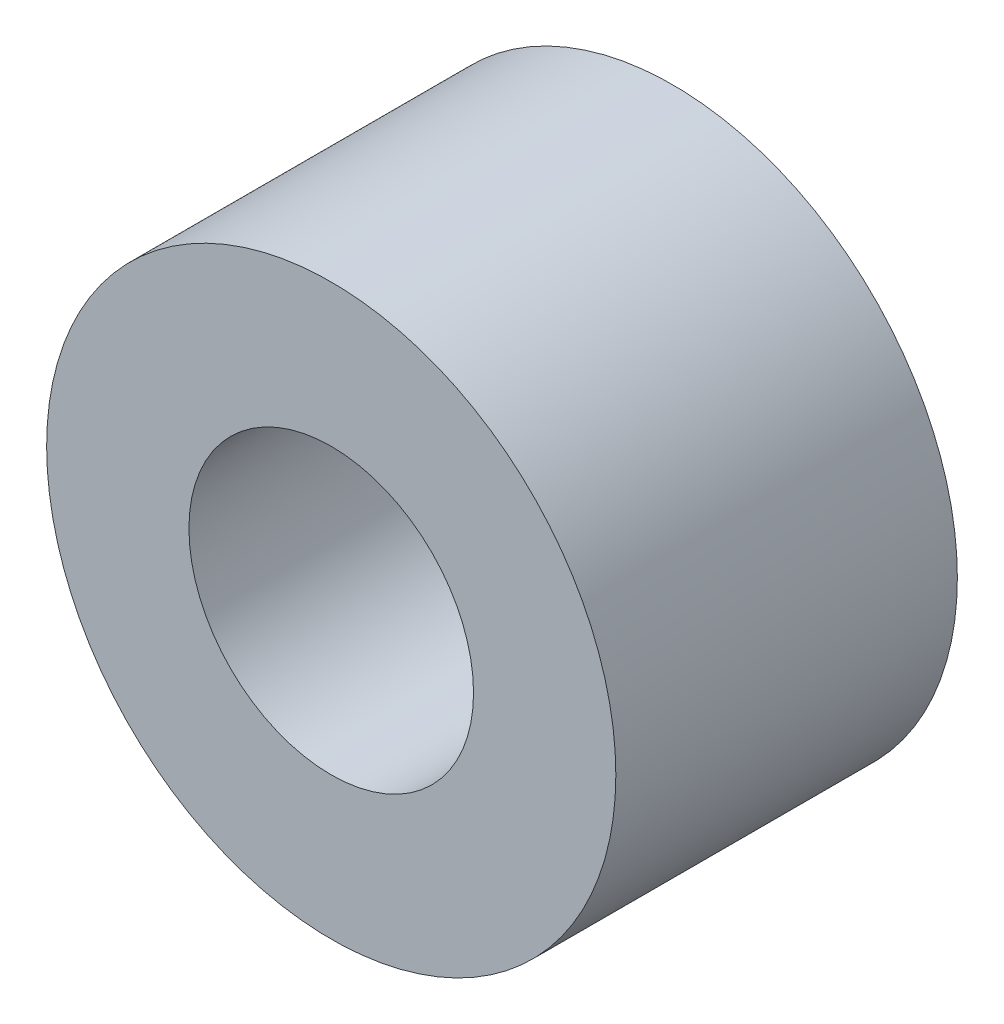
SolidWorks part; units mm, degrees
ref_plane "Front Plane" through (0, 0, 0) normal (0, 0, 1) x (1, 0, 0)
ref_plane "Top Plane" through (0, 0, 0) normal (0, 1, 0) x (1, 0, 0)
ref_plane "Right Plane" through (0, 0, 0) normal (1, 0, 0) x (0, 0, -1)
sketch "Sketch1" plane through (0, 0, 0) normal (0, 0, 1) x (1, 0, 0)
  circle A0 centre (0, 0) radius 2.5
  circle A1 centre (0, 0) radius 5
  dimension "D1" = 10
  dimension "D2" = 5
extrude "Boss-Extrude1" add sketch "Sketch1" along normal blind 6
